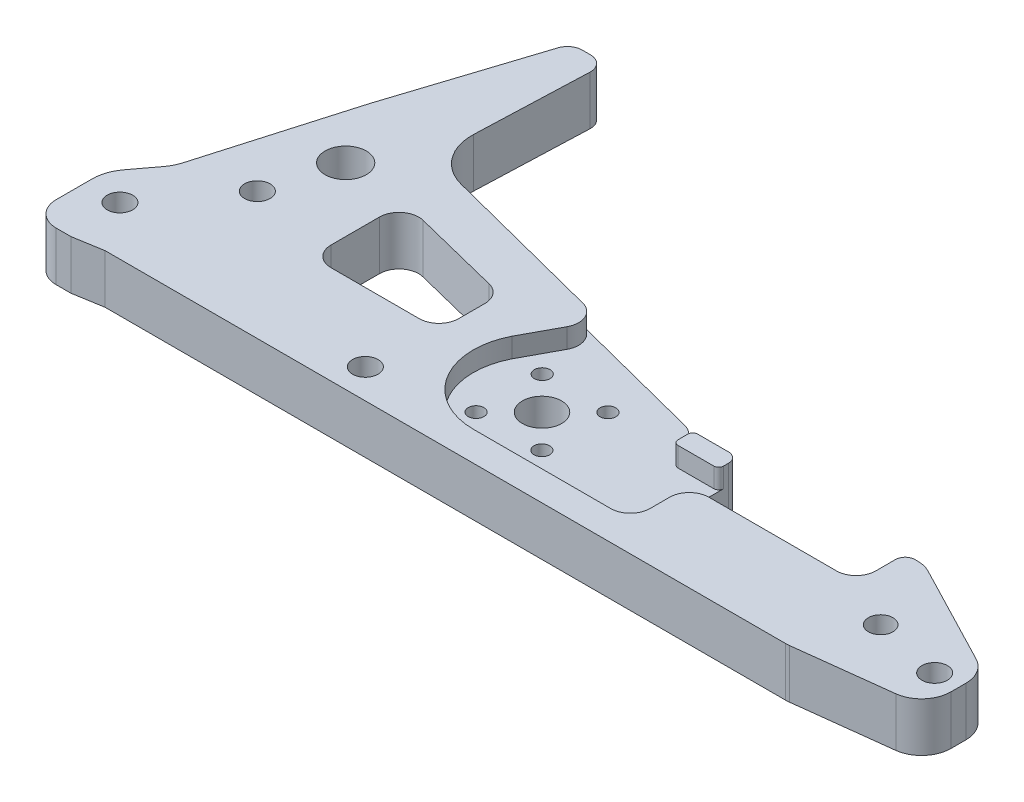
SolidWorks part; units mm, degrees
material "PE High Density"
ref_plane "Front Plane" through (0, 0, 0) normal (0, 0, 1) x (1, 0, 0)
ref_plane "Top Plane" through (0, 0, 0) normal (0, 1, 0) x (1, 0, 0)
ref_plane "Right Plane" through (0, 0, 0) normal (1, 0, 0) x (0, 0, -1)
sketch "Sketch1" plane through (0, 0, 0) normal (0, 1, 0) x (1, 0, 0)
  line L0 (164, 15) -> (139, 28)
  line L5 (164, 3) -> (139, 0)
  line L7 (-14, 14) -> (-14, 2)
  line L9 (0, 0) -> (139, 0)
  line L10 (164, 3) -> (164, 15)
  line L13 (91.7162, 28) -> (139, 28)
  line L15 (1, 53) -> (11, 84)
  line L16 (11, 84) -> (18, 84)
  line L18 (-14, 2) -> (-14, -1)
  line L19 (-14, -1) -> (-6, -1)
  line L22 (-6, -1) -> (0, 0)
  line L23 (16.7162, 50) -> (86.7162, 32)
  line L24 (86.7162, 32) -> (91.7162, 28)
  line L25 (18, 84) -> (16.7162, 50)
  line L26 (-14, 14) -> (-8, 22)
  line L27 (-8, 22) -> (1, 53)
  circle A0 centre (-7, 10) radius 2.6
  circle A3 centre (159, 10) radius 2.6
  circle A4 centre (5, 26) radius 2.6
  circle A6 centre (9, 40) radius 4.2
  circle A8 centre (145, 13) radius 2.5
  dimension "D9" = 5.2
  dimension "D12" = 5
  dimension "D15" = 16
  dimension "D13" = 5.2
  dimension "D17" = 5.2
  dimension "D20" = 6
  dimension "D23" = 8.4
  dimension "D27" = 10
  dimension "D3" = 44
  dimension "D4" = 3
  dimension "D5" = 25
  dimension "D6" = 25
  dimension "D7" = 166
  dimension "D8" = 12
  dimension "D10" = 7
  dimension "D11" = 8
  dimension "D14" = 40
  dimension "D16" = 5
  dimension "D18" = 7
  dimension "D19" = 12
  dimension "D21" = 10
  dimension "D22" = 75
  dimension "D24" = 18
  dimension "D25" = 15
  dimension "D26" = 16
  dimension "D28" = 12
  dimension "D29" = 10
  dimension "D30" = 3
  dimension "D31" = 8
  dimension "D32" = 70
  dimension "D33" = 8
  dimension "D34" = 14
  dimension "D35" = 6
  dimension "D38" = 4
  dimension "D39" = 28
  dimension "D40" = 13
extrude "Boss-Extrude1" add sketch "Sketch1" along normal blind 10
fillet "Fillet2" radius 6 4 edges at (139, 5, 0) (164, 5, -3) (164, 5, -15) (139, 5, -28)
fillet "Fillet3" radius 3 2 edges at (11, 5, -84) (18, 5, -84)
sketch "Sketch4" plane through (0, 10, 0) normal (0, 1, 0) x (1, 0, 0)
  line L0 (22, 39) -> (22, 20)
  line L6 (22, 39) -> (48, 32.5)
  line L7 (48, 32.5) -> (48, 20)
  line L21 (48, 20) -> (22, 20)
  circle A0 centre (9, 40) radius 4.2 construction
  dimension "D1" = 13
  dimension "D2" = 1
  dimension "D3" = 19
  dimension "D5" = 26
  dimension "D8" = 12.5
extrude "Cut-Extrude1" cut sketch "Sketch4" against normal through all
sketch "Sketch7" plane through (0, 10, 0) normal (0, 1, 0) x (1, 0, 0)
  circle A0 centre (47, 6) radius 2.6
  circle A1 centre (9, 40) radius 4.2 construction
  dimension "D3" = 5.2
  dimension "D1" = 6
  dimension "D2" = 38
extrude "Cut-Extrude4" cut sketch "Sketch7" against normal through all
fillet "Fillet8" radius 5 1 edges at (-14, 5, 1)
fillet "Fillet9" radius 4 4 edges at (22, 5, -20) (48, 5, -32.5) (22, 5, -39) (48, 5, -20)
sketch "Sketch10" plane through (0, 10, 0) normal (0, 1, 0) x (1, 0, 0)
  line L0 (101, 28) -> (101, 18)
  line L1 (137.5332, 28) -> (91.7162, 28) construction
  line L2 (101, 18) -> (135, 18)
  line L3 (135, 18) -> (135, 28)
  line L4 (135, 28) -> (101, 28)
  circle A0 centre (9, 40) radius 4.2 construction
  dimension "D1" = 10
  dimension "D2" = 0
  dimension "D3" = 92
  dimension "D4" = 34
extrude "Cut-Extrude6" cut sketch "Sketch10" against normal through all
fillet "Fillet11" radius 2 2 edges at (135, 5, -28) (101, 5, -28)
sketch "Sketch12" plane through (0, 10, 0) normal (0, 1, 0) x (1, 0, 0)
  line L4 (86.7162, 32) -> (16.7162, 50) construction
  line L6 (86.7162, 32) -> (91.7162, 28)
  line L7 (91.7162, 28) -> (91.7162, 24)
  line L8 (91.7162, 24) -> (101, 24)
  line L9 (56.5226, 26.3494) -> (62.8829, 38.1286)
  line L10 (101, 26) -> (101, 18) construction
  line L11 (101, 24) -> (101, 6)
  line L12 (101, 6) -> (69, 6)
  line L13 (62.8829, 38.1286) -> (86.7162, 32)
  circle A2 centre (-7, 10) radius 2.6 construction
  arc A4 (69, 6) -> (56.5226, 26.3494) centre (69, 20) cw
  dimension "D3" = 4
  dimension "D1" = 76
  dimension "D2" = 10
extrude "Cut-Extrude7" cut sketch "Sketch12" against normal blind 4
fillet "Fillet13" radius 10 1 edges at (16.7162, 5, -50)
fillet "Fillet14" radius 4 2 edges at (91.7162, 3, -28) (86.7162, 3, -32)
fillet "Fillet15" radius 1 3 edges at (101, 8, -24) (91.7162, 8, -28) (91.7162, 8, -24)
fillet "Fillet16" radius 4 2 edges at (101, 8, -18) (62.8829, 8, -38.1286)
fillet "Fillet17" radius 4 3 edges at (101, 3, -18) (101, 8, -6) (135, 5, -18)
sketch "Sketch13" plane through (0, 6, 0) normal (0, 1, 0) x (1, 0, 0)
  circle A0 centre (69, 20) radius 4
  dimension "D1" = 8
extrude "Cut-Extrude8" cut sketch "Sketch13" against normal blind 10
fillet "Fillet19" radius 8 2 edges at (-8, 5, -22) (-14, 5, -14)
sketch "Sketch14" plane through (0, 6, 0) normal (0, 1, 0) x (1, 0, 0)
  circle A0 centre (62.3, 26.735) radius 1.6
  circle A2 centre (69, 20) radius 4 construction
  circle A3 centre (75.735, 26.7) radius 1.6
  circle A4 centre (75.7, 13.265) radius 1.6
  circle A5 centre (62.265, 13.3) radius 1.6
  point P13 (69, 20)
  dimension "D2" = 3.2
  dimension "D1" = 9.5
  dimension "D3" = 6.7
  dimension "D4" = 4
extrude "Cut-Extrude9" cut sketch "Sketch14" against normal blind 10
sketch "Sketch15" plane through (0, 0, -28) normal (0, 0, -1) x (-1, 0, 0)
  line L0 (-99, 10) -> (-99, 0) construction
  circle A0 centre (-96.5, 5) radius 1.3
  dimension "D2" = 2.6
  dimension "D1" = 2.5
extrude "Cut-Extrude10" [suppressed] cut sketch "Sketch15" against normal blind 5
